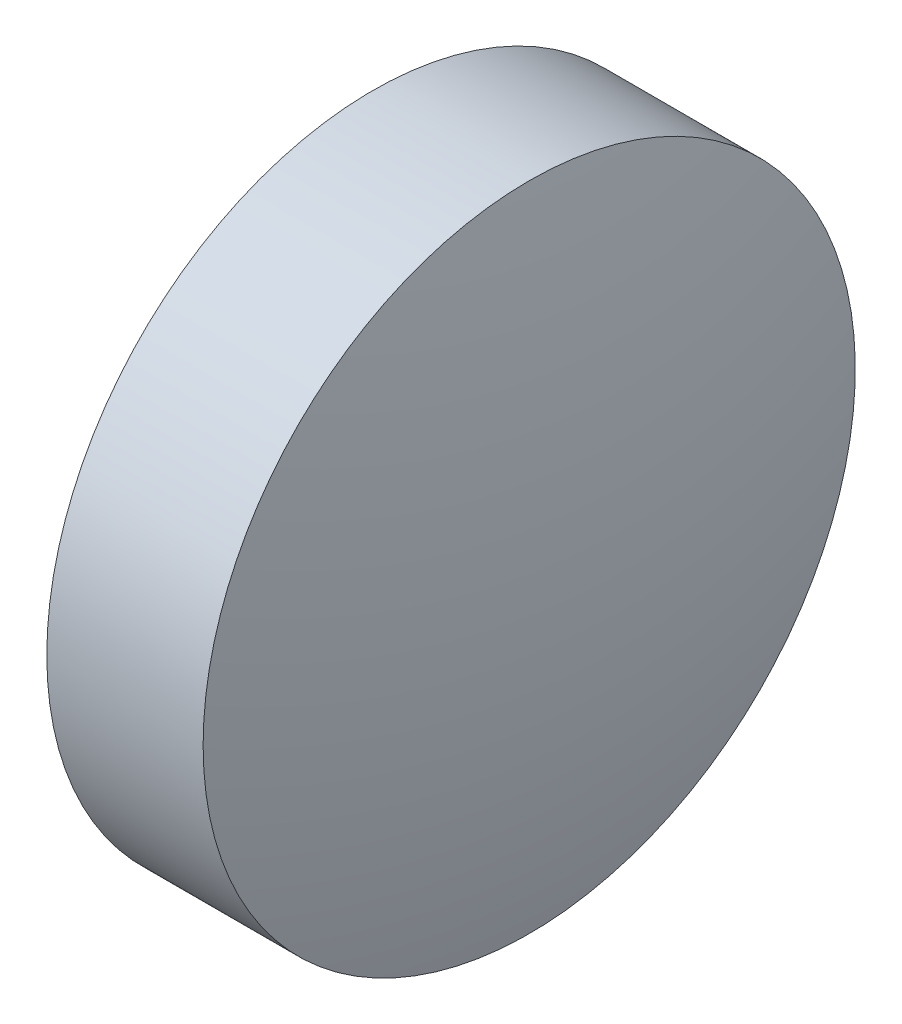
SolidWorks part; units mm, degrees
ref_plane "前视基准面" through (0, 0, 0) normal (0, 0, 1) x (1, 0, 0)
ref_plane "上视基准面" through (0, 0, 0) normal (0, 1, 0) x (1, 0, 0)
ref_plane "右视基准面" through (0, 0, 0) normal (1, 0, 0) x (0, 0, -1)
sketch "草图1" plane through (0, 0, 0) normal (0, 0, 1) x (1, 0, 0)
  line L0 (447.0229, 67.5874) -> (453.1583, 67.5874) construction
  line L1 (447.8845, 67.5874) -> (447.8845, 70.7374)
  line L2 (449.7845, 67.5874) -> (447.8845, 67.5874)
  line L5 (447.8845, 70.7374) -> (449.3945, 70.7374)
  arc A0 (449.7845, 67.5874) -> (449.3945, 70.7374) centre (436.8684, 67.5874) ccw
revolve "旋转1" add sketch "草图1" angle 360 about L0
